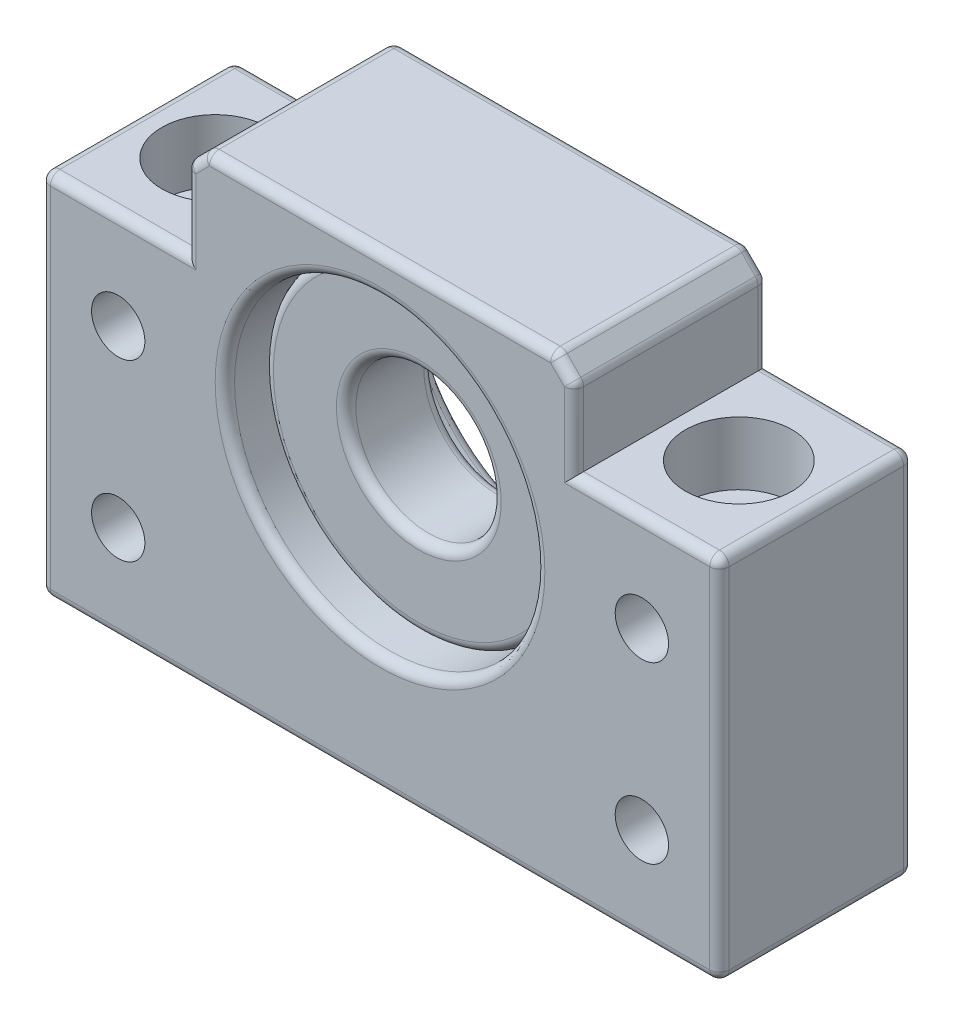
SolidWorks part; units mm, degrees
material "Plain Carbon Steel"
ref_plane "Front Plane" through (0, 0, 0) normal (0, 0, 1) x (1, 0, 0)
ref_plane "Top Plane" through (0, 0, 0) normal (0, 1, 0) x (1, 0, 0)
ref_plane "Right Plane" through (0, 0, 0) normal (1, 0, 0) x (0, 0, -1)
sketch "Sketch2" plane through (0, 0, 0) normal (0, 0, 1) x (1, 0, 0)
  line L0 (0, 0) -> (0, -28) construction
  line L3 (-35, 10) -> (-20, 10)
  line L4 (-35, 10) -> (-35, -28)
  line L5 (-35, -28) -> (35, -28)
  line L6 (35, 10) -> (35, -28)
  line L7 (-20, 20) -> (20, 20)
  line L8 (-20, 20) -> (-20, 10)
  line L9 (20, 20) -> (20, 10)
  line L10 (20, 10) -> (35, 10)
  line L11 (-35, 0) -> (35, 0) construction
  line L12 (0, 0) -> (0, 20) construction
  line L14 (-20, 10) -> (-20, 0) construction
  line L15 (20, 10) -> (20, 0) construction
  dimension "B" = 70
  dimension "h" = 28
  dimension "H1" = 38
  dimension "H2" = 48
  dimension "B1" = 40
extrude "Boss-Extrude1" add sketch "Sketch2" along normal blind 20
sketch "Sketch11" plane through (0, 0, 0) normal (0, 0, 1) x (1, 0, 0)
  line L0 (-27, 37.7108) -> (27, 37.7108) construction
  line L1 (0, 37.7108) -> (0, 0) construction
  line L2 (27, 37.7108) -> (27, 10) construction
  line L3 (-27, 37.7108) -> (-27, 10) construction
  line L4 (-20, 10) -> (-35, 10) construction
  line L5 (-27, 10) -> (-27, -28) construction
  line L6 (-35, -28) -> (35, -28) construction
  line L7 (35, 10) -> (20, 10) construction
  line L8 (27, 10) -> (27, -28) construction
  point P3 (0, 37.7108)
  dimension "P" = 54
sketch "Sketch12" plane through (0, 10, 0) normal (0, 1, 0) x (1, 0, 0)
  line L0 (-27, 0) -> (-27, -20) construction
  line L3 (-20, -20) -> (-35, -20) construction
  line L4 (27, 0) -> (27, -20) construction
  line L5 (35, -20) -> (20, -20) construction
  line L6 (-35, -10) -> (35, -10) construction
  line L9 (-35, -20) -> (-35, 0) construction
  line L10 (35, -20) -> (35, 0) construction
  circle A0 centre (-27, -10) radius 3.3
  circle A1 centre (27, -10) radius 3.3
  dimension "X" = 6.6
extrude "Cut-Extrude3" cut sketch "Sketch12" against normal blind 100
sketch "Sketch13" plane through (0, 0, 0) normal (0, 0, 1) x (1, 0, 0)
  line L0 (-27, 0) -> (27, 0) construction
  line L1 (-27, 10) -> (-27, -28) construction
  line L2 (27, 10) -> (27, -28) construction
  line L3 (-27, -18) -> (27, -18) construction
  line L4 (0, 0) -> (0, -18) construction
  line L5 (0, -18) -> (0, -28) construction
  line L6 (-35, -28) -> (35, -28) construction
  line L7 (0, 0) -> (0, 20) construction
  line L8 (20, 20) -> (-20, 20) construction
  circle A0 centre (-27, 0) radius 2.75
  circle A1 centre (-27, -18) radius 2.75
  circle A2 centre (27, -18) radius 2.75
  circle A3 centre (27, 0) radius 2.75
  circle A4 centre (0, 0) radius 16
  dimension "D1" = 32
  dimension "d2" = 5.5
  dimension "E" = 18
extrude "Cut-Extrude4" cut sketch "Sketch13" along normal blind 50
sketch "Sketch14" plane through (0, 10, 0) normal (0, 1, 0) x (1, 0, 0)
  circle A0 centre (-27, -10) radius 5.5
  circle A1 centre (27, -10) radius 5.5
  dimension "Y" = 11
extrude "Cut-Extrude5" cut sketch "Sketch14" against normal blind 6.5
sketch "Sketch16" plane through (0, 0, 0) normal (0, 0, 1) x (1, 0, 0)
  circle A0 centre (0, 0) radius 16
  circle A1 centre (0, 0) radius 7.5
  dimension "D1" = 32
  dimension "D2" = 15
extrude "Boss-Extrude3" add sketch "Sketch16" along normal blind 9 from offset 7 separate body
chamfer "Chamfer1" distance 2 angle 45 2 edges at (-20, 20, 10) (20, 20, 10)
fillet "Fillet1" radius 1 30 edges at (16, 0, 0) (16, 0, 20) (35, -28, 10) (-35, -28, 10) (-35, 10, 10) (35, 10, 10) (-27.5, 10, 20) (-27.5, 10, 0) (0, 20, 20) (0, 20, 0) (27.5, 10, 20) (27.5, 10, 0) (0, -28, 20) (0, -28, 0) (-35, -9, 20) (-35, -9, 0) (35, -9, 20) (35, -9, 0) (19, 19, 0) (20, 14, 0) (20, 14, 20) (19, 19, 20) (-20, 14, 0) (-19, 19, 0) (-20, 14, 20) (-19, 19, 20) (20, 18, 10) (18, 20, 10) (-20, 18, 10) (-18, 20, 10)
fillet "Fillet2" radius 1 4 edges at (7.5, 0, 16) (7.5, 0, 7) (16, 0, 7) (16, 0, 16)
equation "\"H\"=95.732"
equation "\"E\"=31.8321"
